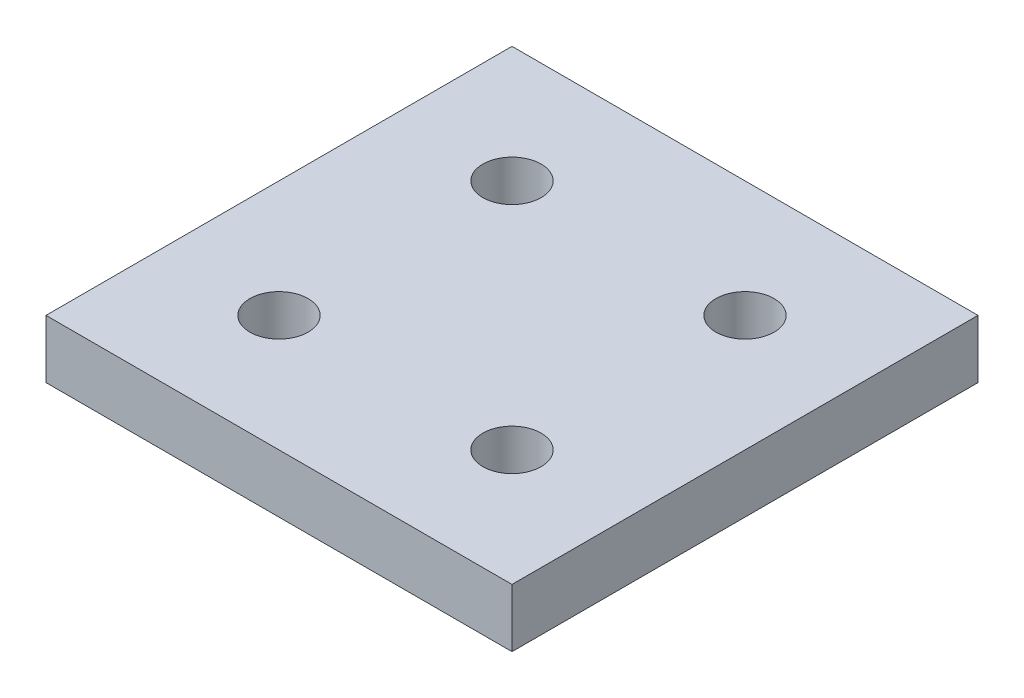
SolidWorks part; units mm, degrees
material "6061 Alloy"
ref_plane "Front Plane" through (0, 0, 0) normal (0, 0, 1) x (1, 0, 0)
ref_plane "Top Plane" through (0, 0, 0) normal (0, 1, 0) x (1, 0, 0)
ref_plane "Right Plane" through (0, 0, 0) normal (1, 0, 0) x (0, 0, -1)
sketch "Sketch1" plane through (0, 0, 0) normal (0, 1, 0) x (1, 0, 0)
  line L0 (40, 0) -> (0, -40) construction
  line L1 (0, 0) -> (40, 0)
  line L2 (0, 0) -> (0, -40)
  line L3 (0, -40) -> (40, -40)
  line L4 (40, 0) -> (40, -40)
  line L5 (0, -20) -> (40, -20) construction
  line L6 (20, 0) -> (20, -40) construction
  circle A0 centre (10, -10) radius 2.5
  circle A4 centre (30, -30) radius 2.5
  circle A5 centre (10, -30) radius 2.5
  circle A6 centre (30, -10) radius 2.5
  dimension "D3" = 5
  dimension "D1" = 40
  dimension "D2" = 40
  dimension "D7" = 10
  dimension "D8" = 10
extrude "Boss-Extrude1" add sketch "Sketch1" along normal blind 5
